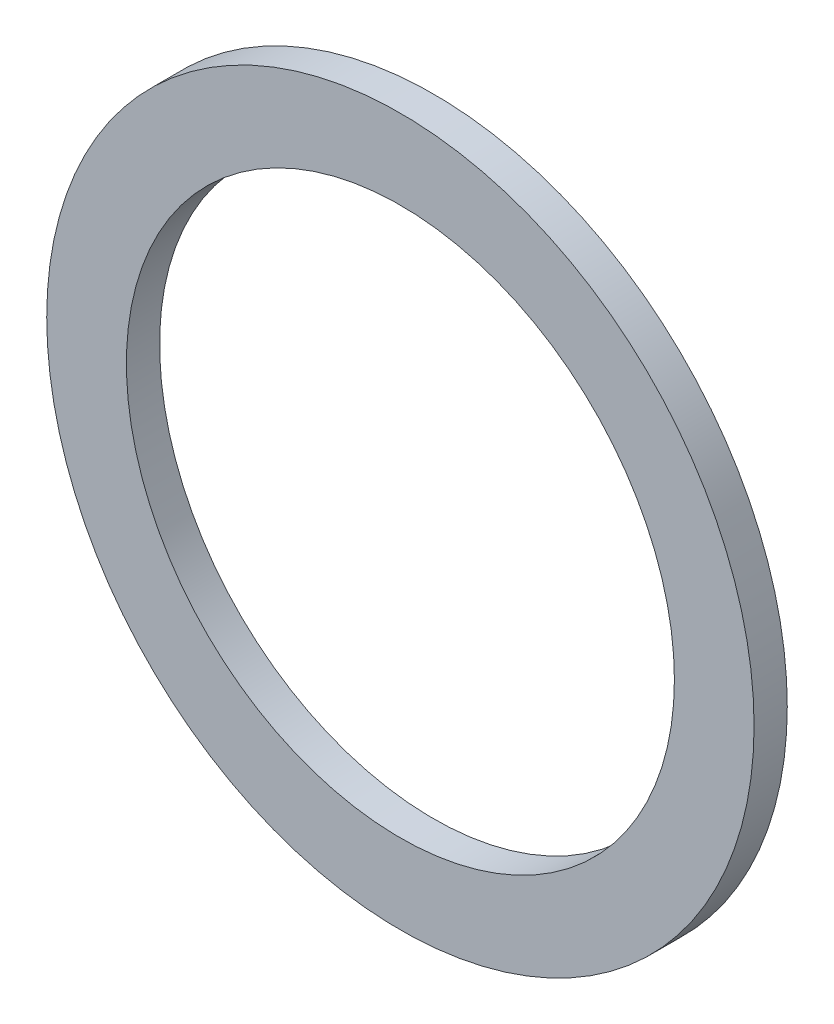
SolidWorks part; units mm, degrees
ref_plane "Front Plane" through (0, 0, 0) normal (0, 0, 1) x (1, 0, 0)
ref_plane "Top Plane" through (0, 0, 0) normal (0, 1, 0) x (1, 0, 0)
ref_plane "Right Plane" through (0, 0, 0) normal (1, 0, 0) x (0, 0, -1)
sketch "Sketch1" plane through (0, 0, 0) normal (0, 0, 1) x (1, 0, 0)
  circle A0 centre (0, 0) radius 4.127
  circle A1 centre (0, 0) radius 5.327
  dimension "D1" = 8.254
  dimension "D2" = 1.2
extrude "Boss-Extrude1" add sketch "Sketch1" along normal blind 0.5
